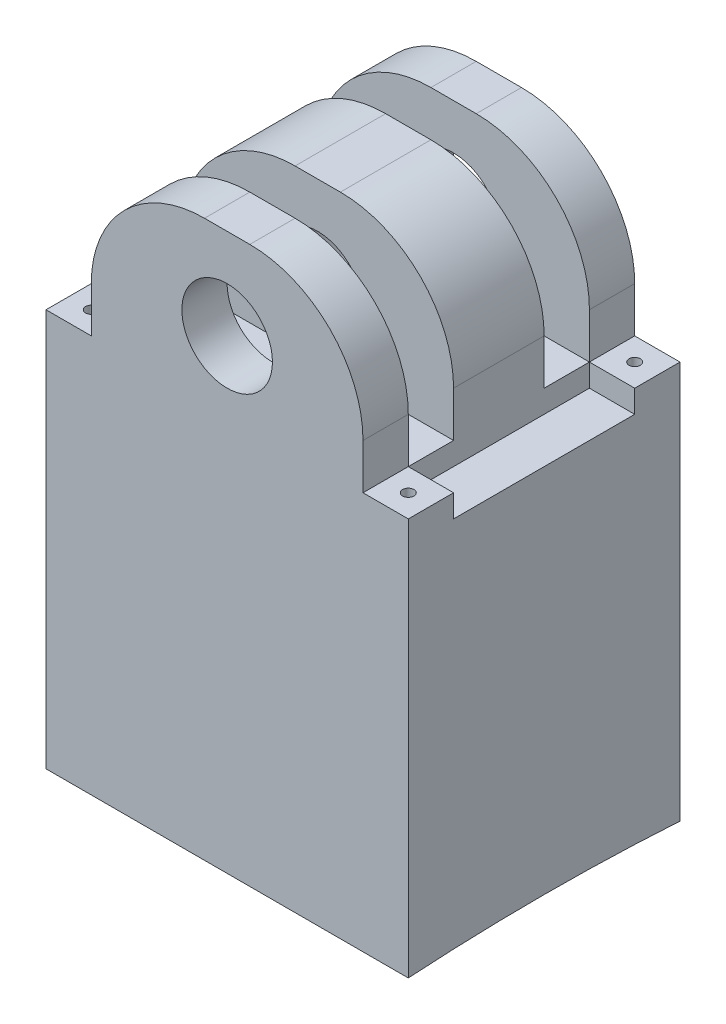
SolidWorks part; units mm, degrees
material "7075-T6 (SN)"
ref_plane "Front Plane" through (0, 0, 0) normal (0, 0, 1) x (1, 0, 0)
ref_plane "Top Plane" through (0, 0, 0) normal (0, 1, 0) x (1, 0, 0)
ref_plane "Right Plane" through (0, 0, 0) normal (1, 0, 0) x (0, 0, -1)
sketch "Sketch1" plane through (0, 0, 0) normal (0, 0, 1) x (1, 0, 0)
  line L0 (-101.6, -50.8) -> (101.6, -50.8)
  line L1 (-76.2, -50.8) -> (76.2, -50.8) construction
  line L2 (-76.2, -38.1) -> (-76.2, -12.7)
  line L3 (-12.7, 50.8) -> (12.7, 50.8)
  line L4 (76.2, -38.1) -> (76.2, -12.7)
  line L5 (-76.2, -50.8) -> (76.2, 50.8) construction
  line L6 (-76.2, 50.8) -> (76.2, -50.8) construction
  line L7 (-76.2, -50.8) -> (-101.6, -50.8) construction
  line L9 (-76.2, -38.1) -> (-101.6, -38.1)
  line L10 (-101.6, -50.8) -> (-101.6, -38.1)
  line L11 (76.2, -50.8) -> (101.6, -50.8) construction
  line L13 (76.2, -38.1) -> (101.6, -38.1)
  line L14 (101.6, -50.8) -> (101.6, -38.1)
  arc A0 (76.2, -12.7) -> (12.7, 50.8) centre (12.7, -12.7) ccw
  arc A1 (-12.7, 50.8) -> (-76.2, -12.7) centre (-12.7, -12.7) ccw
  circle A2 centre (0, 0) radius 25.4
  point P0 (0, 0)
  dimension "D3" = 63.5
  dimension "D8" = 50.8
  dimension "D1" = 152.4
  dimension "D2" = 101.6
  dimension "D4" = 12.7
  dimension "D5" = 12.7
  dimension "D6" = 25.4
  dimension "D7" = 25.4
extrude "Boss-Extrude1" add sketch "Sketch1" along normal blind 152.4
sketch "Sketch3" plane through (0, 0, 0) normal (1, 0, 0) x (0, 0, -1)
  line L0 (-152.4, -38.1) -> (0, -38.1) construction
  line L1 (-127, -38.1) -> (-101.6, -38.1)
  line L2 (-127, -38.1) -> (-127, 50.8)
  line L3 (-127, 50.8) -> (-101.6, 50.8)
  line L4 (-101.6, -38.1) -> (-101.6, 50.8)
  line L5 (-152.4, 50.8) -> (0, 50.8) construction
  line L6 (-152.4, 50.8) -> (-152.4, -12.7) construction
  line L7 (-50.8, -38.1) -> (-25.4, -38.1)
  line L8 (-50.8, -38.1) -> (-50.8, 50.8)
  line L9 (-50.8, 50.8) -> (-25.4, 50.8)
  line L10 (-25.4, -38.1) -> (-25.4, 50.8)
  dimension "D1" = 25.4
  dimension "D2" = 25.4
  dimension "D3" = 50.8
  dimension "D4" = 25.4
extrude "Cut-Extrude1" cut sketch "Sketch3" against normal through all both and the other way through all
sketch "Sketch4" plane through (0, -38.1, 0) normal (0, 1, 0) x (1, 0, 0)
  line L0 (-101.6, -152.4) -> (-101.6, 0) construction
  line L1 (101.6, -152.4) -> (101.6, 0) construction
  line L2 (-76.2, 0) -> (-101.6, 0) construction
  line L3 (-76.2, -101.6) -> (-76.2, -50.8) construction
  line L4 (-101.6, -25.4) -> (-76.2, -25.4)
  line L5 (-101.6, -25.4) -> (-101.6, -127)
  line L6 (-101.6, -127) -> (-76.2, -127)
  line L7 (-76.2, -25.4) -> (-76.2, -127)
  line L8 (-76.2, -152.4) -> (-101.6, -152.4) construction
  line L9 (0, -55) -> (0, 55) construction
  line L10 (101.6, -127) -> (76.2, -127)
  line L11 (76.2, -25.4) -> (76.2, -127)
  line L12 (101.6, -25.4) -> (76.2, -25.4)
  line L13 (101.6, -25.4) -> (101.6, -127)
  point P0 (-88.9, -12.7)
  point P2 (-88.9, -139.7)
  point P3 (88.9, -12.7)
  point P5 (88.9, -139.7)
  dimension "D1" = 12.7
  dimension "D2" = 12.7
  dimension "D3" = 12.7
  dimension "D4" = 25.4
  dimension "D5" = 25.4
hole_wizard "1/4 (0.25) Diameter Hole1" positions "Sketch5" profile "Sketch6" hole size "1/4" standard "ANSI Inch" end condition through all
sketch "Sketch5" plane through (0, -38.1, 0) normal (0, 1, 0) x (1, 0, 0)
  point P3 (-88.9, -12.7)
  point P6 (-88.9, -139.7)
  point P9 (88.9, -12.7)
  point P15 (88.9, -139.7)
sketch "Sketch6" plane through (-88.9, -38.1, 12.7) normal (1, 0, 0) x (0, 0, 1)
  line L0 (0, 0) -> (0, 12.7)
  line L1 (0, 12.7) -> (3.175, 12.7)
  line L2 (3.175, 12.7) -> (3.175, 0)
  line L5 (3.175, 0) -> (0, 0)
  line L11 (0, -6.35) -> (0, 107.95) construction
  dimension "Thru Hole Dia." = 6.35
  dimension "Thru Hole Depth" = 12.7
extrude "Cut-Extrude2" cut sketch "Sketch4" against normal through all
sketch "Sketch7" plane through (0, 0, 0) normal (0, 0, -1) x (-1, 0, 0)
  line L1 (-101.6, -50.8) -> (101.6, -50.8)
  line L2 (-101.6, -50.8) -> (-101.6, -261.1095)
  line L3 (-101.6, -261.1095) -> (101.6, -261.1095)
  line L4 (101.6, -50.8) -> (101.6, -261.1095)
extrude "Boss-Extrude2" add sketch "Sketch7" against normal up to surface (152.4 mm away) up to face at (0, -15.1497, 152.4)
sketch "Sketch8" plane through (101.6, 0, 0) normal (1, 0, 0) x (0, 0, -1)
  line L0 (-152.4, -261.1095) -> (0, -261.1095)
  arc A0 (-152.4, -261.1095) -> (0, -261.1095) centre (-76.2, -1458.6877) cw
  dimension "D1" = 1200
extrude "Cut-Extrude3" cut sketch "Sketch8" against normal through all contours A0 L0
